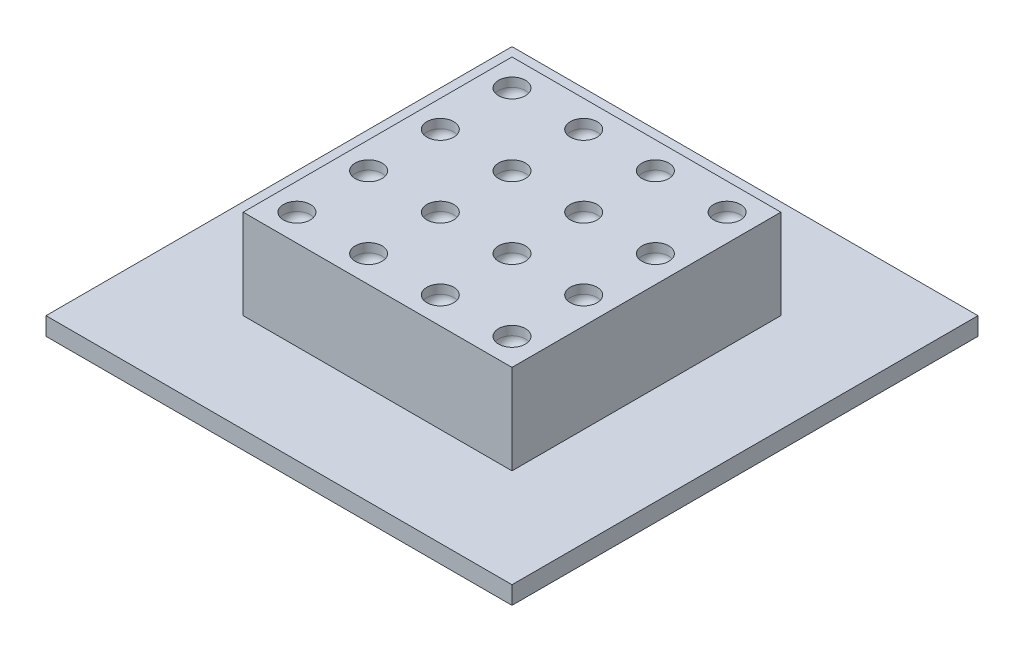
SolidWorks part; units mm, degrees
ref_plane "Front Plane" through (0, 0, 0) normal (0, 0, 1) x (1, 0, 0)
ref_plane "Top Plane" through (0, 0, 0) normal (0, 1, 0) x (1, 0, 0)
ref_plane "Right Plane" through (0, 0, 0) normal (1, 0, 0) x (0, 0, -1)
sketch "Sketch1" plane through (0, 0, 0) normal (0, 1, 0) x (1, 0, 0)
  line L1 (7.5, -7.5) -> (-7.5, -7.5)
  line L2 (7.5, -7.5) -> (7.5, 7.5)
  line L3 (7.5, 7.5) -> (-7.5, 7.5)
  line L4 (-7.5, -7.5) -> (-7.5, 7.5)
  line L5 (7.5, -7.5) -> (-7.5, 7.5) construction
  line L6 (7.5, 7.5) -> (-7.5, -7.5) construction
  point P0 (0, 0)
  dimension "D1" = 15
extrude "Boss-Extrude1" add sketch "Sketch1" along normal blind 5
sketch "Sketch2" plane through (0, 0, 0) normal (0, -1, 0) x (1, 0, 0)
  line L8 (-13, 13) -> (-13, -13)
  line L9 (-13, -13) -> (13, -13)
  line L10 (13, -13) -> (13, 13)
  line L11 (13, 13) -> (-13, 13)
  line L12 (-13, 13) -> (-13, -13)
  line L13 (-13, -13) -> (13, -13)
  line L14 (13, -13) -> (13, 13)
  line L15 (13, 13) -> (-13, 13)
  dimension "D1" = 5.5
extrude "Boss-Extrude2" add sketch "Sketch2" along normal blind 1
sketch "Sketch3" plane through (0, 5, 0) normal (0, 1, 0) x (1, 0, 0)
  line L0 (7.5, 7.5) -> (-7.5, 7.5) construction
  line L1 (-7.5, 7.5) -> (-7.5, -7.5) construction
  circle A0 centre (-6, 6) radius 0.75
  dimension "D1" = 1.5
  dimension "D2" = 1.5
  dimension "D3" = 1.5
extrude "Cut-Extrude1" cut sketch "Sketch3" against normal blind 1
fillet "Fillet1" radius 0.5 1 edges at (-6, 4, -5.25)
pattern_linear "LPattern1" count 4 spacing 4 along (1, 0, 0) count 4 spacing 4 along (0, 0, 1) of "Cut-Extrude1", "Fillet1"
